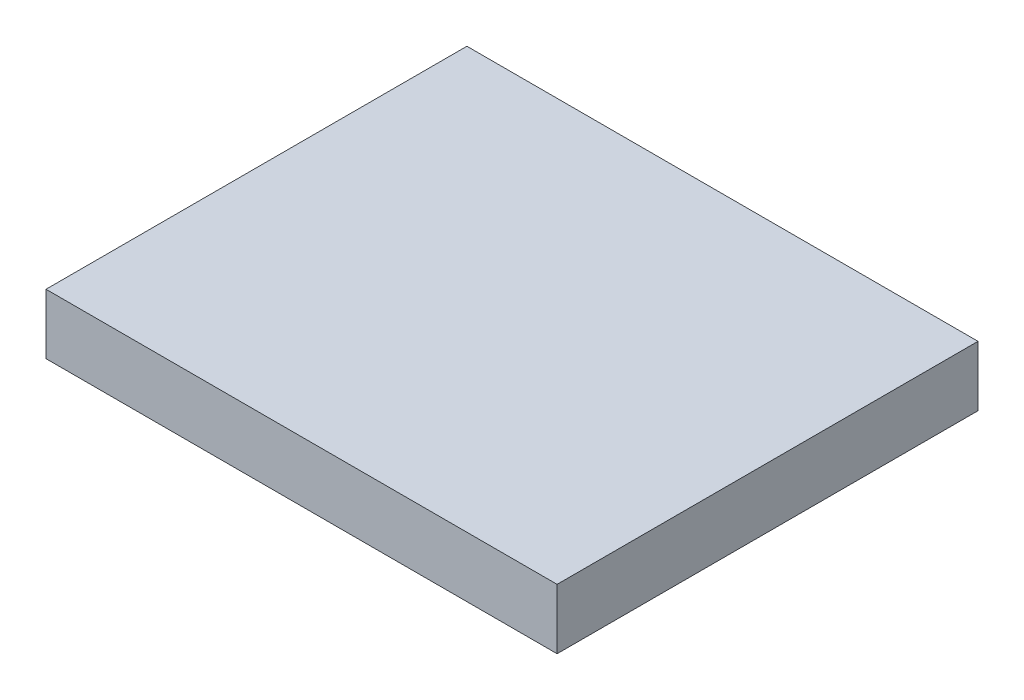
SolidWorks part; units mm, degrees
material "paste"
ref_plane "Front Plane" through (0, 0, 0) normal (0, 0, 1) x (1, 0, 0)
ref_plane "Top Plane" through (0, 0, 0) normal (0, 1, 0) x (1, 0, 0)
ref_plane "Right Plane" through (0, 0, 0) normal (1, 0, 0) x (0, 0, -1)
sketch "Sketch1" plane through (0, 0, 0) normal (0, 1, 0) x (1, 0, 0)
  line L1 (-11.9676, 6.8486) -> (5.0324, 6.8486)
  line L2 (-11.9676, 6.8486) -> (-11.9676, -7.1514)
  line L3 (-11.9676, -7.1514) -> (5.0324, -7.1514)
  line L4 (5.0324, 6.8486) -> (5.0324, -7.1514)
  dimension "D1" = 14
  dimension "D2" = 17
sketch "Sketch2" plane through (0, 0, 0) normal (0, 1, 0) x (1, 0, 0)
  line L0 (-11.9676, 6.8486) -> (5.0324, 6.8486)
  line L1 (-11.9676, 6.8486) -> (-11.9676, -7.1514)
  line L2 (-11.9676, -7.1514) -> (5.0324, -7.1514)
  line L3 (5.0324, 6.8486) -> (5.0324, -7.1514)
extrude "Boss-Extrude1" add sketch "Sketch2" along normal blind 2
